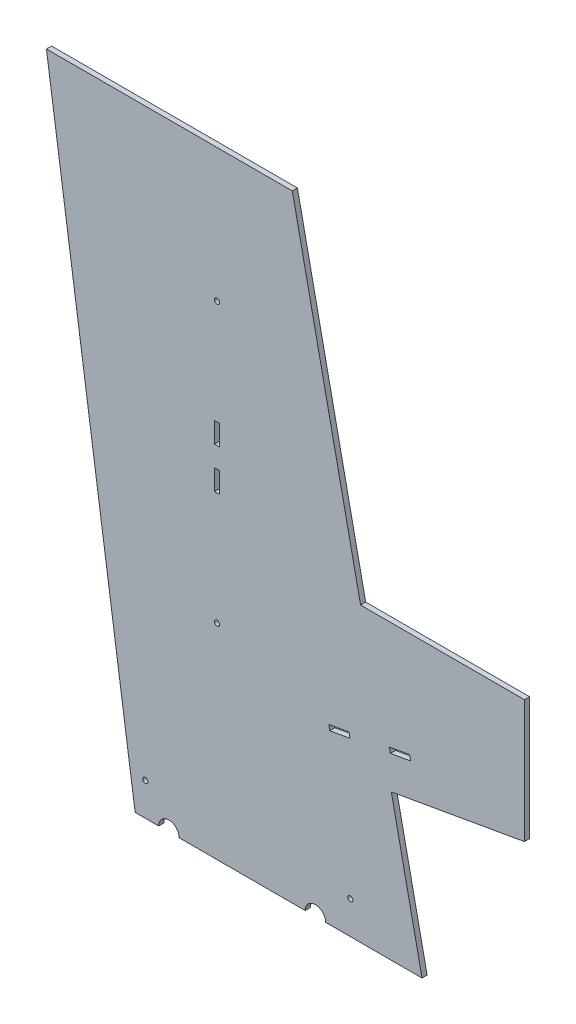
SolidWorks part; units mm, degrees
ref_plane "Front Plane" through (0, 0, 0) normal (0, 0, 1) x (1, 0, 0)
ref_plane "Top Plane" through (0, 0, 0) normal (0, 1, 0) x (1, 0, 0)
ref_plane "Right Plane" through (0, 0, 0) normal (1, 0, 0) x (0, 0, -1)
sketch "Sketch1" plane through (0, 0, 0) normal (0, 0, 1) x (1, 0, 0)
  line L0 (0, 0) -> (-177.8, 0)
  line L1 (-177.8, 0) -> (-232.7656, 382.27)
  line L2 (-232.7656, 382.27) -> (-80.3656, 382.27)
  line L3 (-80.3656, 382.27) -> (0, 0)
  dimension "D1" = 382.27
  dimension "D2" = 177.8
  dimension "D3" = 152.4
  dimension "D4" = 54.9656
extrude "Boss-Extrude1" add sketch "Sketch1" along normal blind 3.175
sketch "Sketch2" plane through (0, 0, 3.175) normal (0, 0, 1) x (1, 0, 0)
  line L0 (-177.8, 0) -> (0, 0) construction
  circle A0 centre (-127, 127) radius 1.5875
  circle A1 centre (-127, 299.72) radius 1.5875
  dimension "D1" = 3.175
  dimension "D2" = 3.175
  dimension "D3" = 172.72
  dimension "D4" = 172.72
  dimension "D5" = 127
  dimension "D6" = 127
extrude "Cut-Extrude1" cut sketch "Sketch2" against normal blind 3.175
sketch "Sketch3" plane through (0, 0, 3.175) normal (0, 0, 1) x (1, 0, 0)
  line L1 (-63.5, 82.55) -> (63.5, 104.9435)
  line L2 (-63.5, 82.55) -> (-63.5, 181.1435)
  line L3 (-63.5, 181.1435) -> (63.5, 181.1435)
  line L4 (63.5, 104.9435) -> (63.5, 181.1435)
  line L5 (-177.8, 0) -> (0, 0) construction
  circle A0 centre (-127, 127) radius 1.5875 construction
  dimension "D1" = 127
  dimension "D2" = 76.2
  dimension "D3" = 44.45
  dimension "D4" = 63.5
  dimension "D5" = 10
extrude "Boss-Extrude2" add sketch "Sketch3" against normal blind 3.175
sketch "Sketch4" plane through (0, 0, 3.175) normal (0, 0, 1) x (1, 0, 0)
  line L0 (-57.15, 104.14) -> (-44.6429, 106.3453)
  line L1 (-45.1943, 109.4721) -> (-57.7013, 107.2668)
  line L2 (-57.7013, 107.2668) -> (-57.15, 104.14)
  line L3 (-45.1943, 109.4721) -> (-44.6429, 106.3453)
  line L4 (-19.6288, 110.756) -> (-7.1218, 112.9613)
  line L5 (-7.6731, 116.0881) -> (-20.1802, 113.8828)
  line L6 (-20.1802, 113.8828) -> (-19.6288, 110.756)
  line L7 (-7.6731, 116.0881) -> (-7.1218, 112.9613)
  line L8 (-19.0041, 90.3958) -> (63.5, 104.9435) construction
  circle A0 centre (-127, 127) radius 1.5875 construction
  dimension "D1" = 3.175
  dimension "D2" = 12.7
  dimension "D3" = 3.175
  dimension "D4" = 12.7
  dimension "D5" = 0
  dimension "D6" = 25.4
  dimension "D7" = 69.85
  dimension "D8" = 22.86
  dimension "D9" = 0
extrude "Cut-Extrude2" cut sketch "Sketch4" against normal blind 3.175
sketch "Sketch5" plane through (0, 0, 3.175) normal (0, 0, 1) x (1, 0, 0)
  line L0 (-127, 127) -> (-127, 299.72)
  line L1 (-128.5875, 196.85) -> (-125.4125, 196.85)
  line L2 (-125.4125, 196.85) -> (-125.4125, 209.55)
  line L3 (-125.4125, 209.55) -> (-128.5875, 209.55)
  line L4 (-128.5875, 209.55) -> (-128.5875, 196.85)
  dimension "D1" = 90
  dimension "D2" = 3.175
  dimension "D3" = 1.5875
  dimension "D4" = 69.85
  dimension "D5" = 12.7
extrude "Cut-Extrude3" cut sketch "Sketch5" against normal blind 10.16 contours L2 L3 L0 L1 | L3 L4 L1 L0
pattern_linear "LPattern1" count 2 spacing 25.4 along (0, 1, 0) of "Cut-Extrude3"
sketch "Sketch9" plane through (0, 0, 0) normal (0, 0, -1) x (-1, 0, 0)
  line L0 (177.8, 0) -> (0, 0) construction
  circle A0 centre (171.45, 20.32) radius 1.5875
  circle A1 centre (44.45, 20.32) radius 1.5875
  dimension "D1" = 3.175
  dimension "D2" = 20.32
  dimension "D3" = 6.35
  dimension "D4" = 3.175
  dimension "D5" = 20.32
  dimension "D6" = 127
extrude "Cut-Extrude7" cut sketch "Sketch9" against normal blind 7.62
sketch "Sketch10" plane through (0, 0, 0) normal (0, 0, -1) x (-1, 0, 0)
  line L0 (177.8, 0) -> (0, 0) construction
  circle A0 centre (156.845, 0) radius 6.35
  circle A1 centre (66.04, 0) radius 6.35
  dimension "D1" = 12.7
  dimension "D2" = 20.955
  dimension "D3" = 90.805
  dimension "D4" = 12.7
extrude "Cut-Extrude8" cut sketch "Sketch10" against normal blind 5.08
